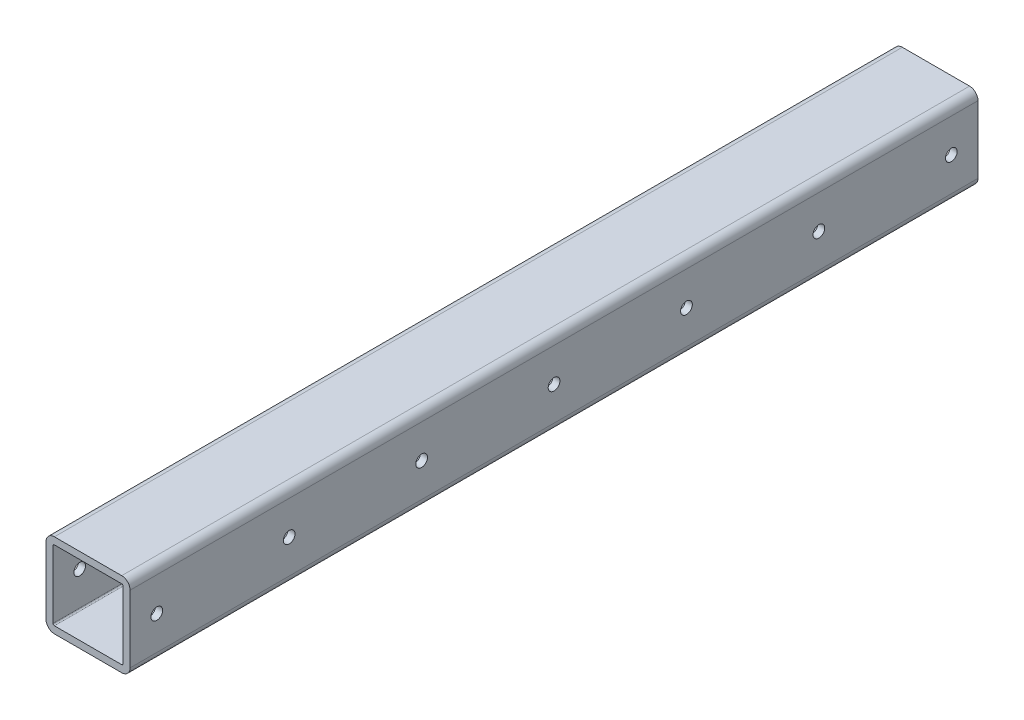
SolidWorks part; units mm, degrees
material "Alloy Steel"
ref_plane "Front Plane" through (0, 0, 0) normal (0, 0, 1) x (1, 0, 0)
ref_plane "Top Plane" through (0, 0, 0) normal (0, 1, 0) x (1, 0, 0)
ref_plane "Right Plane" through (0, 0, 0) normal (1, 0, 0) x (0, 0, -1)
sketch "Sketch1" plane through (0, 0, 0) normal (0, 0, 1) x (1, 0, 0)
  line L1 (-15.875, 15.875) -> (15.875, 15.875)
  line L2 (-15.875, 15.875) -> (-15.875, -15.875)
  line L3 (-15.875, -15.875) -> (15.875, -15.875)
  line L4 (15.875, 15.875) -> (15.875, -15.875)
  line L5 (-15.875, 15.875) -> (15.875, -15.875) construction
  line L6 (-15.875, -15.875) -> (15.875, 15.875) construction
  line L7 (-19.05, 19.05) -> (19.05, 19.05)
  line L8 (-19.05, 19.05) -> (-19.05, -19.05)
  line L9 (-19.05, -19.05) -> (19.05, -19.05)
  line L10 (19.05, 19.05) -> (19.05, -19.05)
  line L11 (-19.05, 19.05) -> (19.05, -19.05) construction
  line L12 (-19.05, -19.05) -> (19.05, 19.05) construction
  point P0 (0, 0)
  point P6 (0, 0)
  dimension "D1" = 38.1
  dimension "D2" = 3.175
  dimension "D3" = 38.1
  dimension "D4" = 3.175
extrude "Boss-Extrude1" add sketch "Sketch1" along normal mid plane 384.175
fillet "Fillet1" radius 3.81 4 edges at (-19.05, -19.05, 0) (-19.05, 19.05, 0) (19.05, -19.05, 0) (19.05, 19.05, 0)
fillet "Fillet2" radius 0.635 4 edges at (15.875, 15.875, 0) (-15.875, 15.875, 0) (-15.875, -15.875, 0) (15.875, -15.875, 0)
sketch "Sketch2" plane through (0, 0, 0) normal (1, 0, 0) x (0, 0, -1)
  line L0 (-192.0875, 0) -> (192.0875, 0) construction
  line L1 (-192.0875, -15.24) -> (-192.0875, 15.24) construction
  line L2 (192.0875, -15.24) -> (192.0875, 15.24) construction
  circle A0 centre (-180, 0) radius 2.65
  circle A1 centre (-120, 0) radius 2.65
  circle A2 centre (-60, 0) radius 2.65
  circle A3 centre (0, 0) radius 2.65
  circle A4 centre (60, 0) radius 2.65
  circle A5 centre (120, 0) radius 2.65
  circle A6 centre (180, 0) radius 2.65
  dimension "D1" = 5.3
  dimension "D2" = 12.0875
  dimension "D3" = 60
  dimension "D4" = 60
  dimension "D5" = 12.0875
  dimension "D6" = 60
  dimension "D7" = 60
  dimension "D8" = 60
extrude "Cut-Extrude1" cut sketch "Sketch2" against normal through all both and the other way through all
